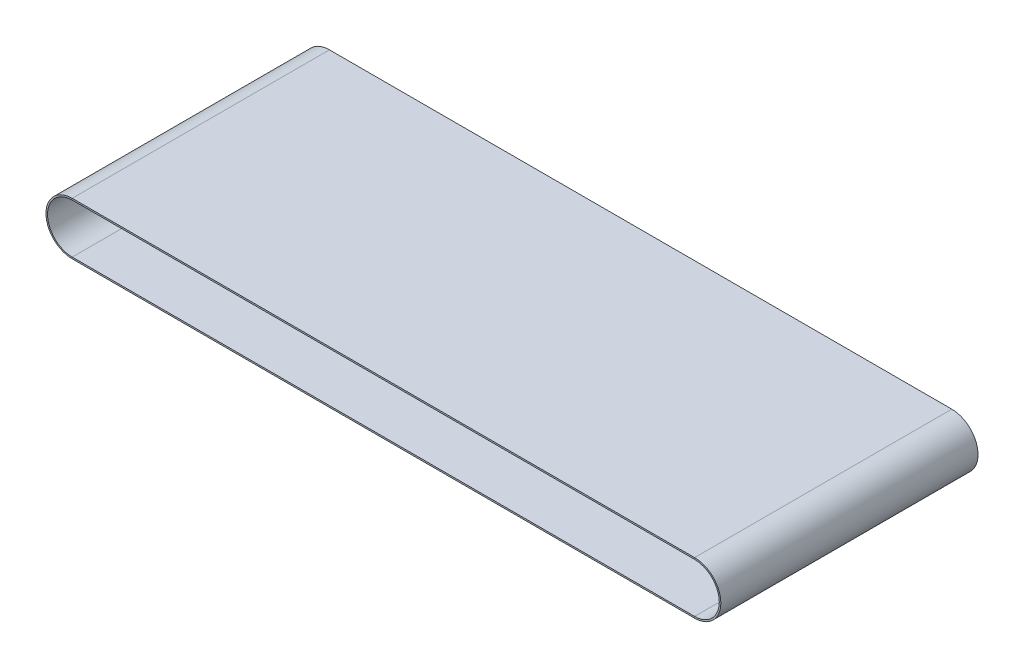
SolidWorks part; units mm, degrees
ref_plane "Front Plane" through (0, 0, 0) normal (0, 0, 1) x (1, 0, 0)
ref_plane "Top Plane" through (0, 0, 0) normal (0, 1, 0) x (1, 0, 0)
ref_plane "Right Plane" through (0, 0, 0) normal (1, 0, 0) x (0, 0, -1)
sketch "Sketch2" plane through (0, 0, 0) normal (0, 0, 1) x (1, 0, 0)
  line L0 (0, 0) -> (1, 0) construction
  line L1 (0, 0) -> (0, 1) construction
  line L2 (0, -24) -> (-605, -24)
  line L3 (-605, 24) -> (0, 24)
  arc A0 (0, 24) -> (0, -24) centre (0, 0) cw
  arc A1 (-605, -24) -> (-605, 24) centre (-605, 0) cw
ref_plane "Plane1" through (-605, 0, 0) normal (1, 0, 0) x (0, 0, -1)
sketch "Sketch4" plane through (-605, 0, 0) normal (1, 0, 0) x (0, 0, -1)
  line L0 (-125, 24) -> (125, 24)
  line L2 (125, 24) -> (125, 25.5)
  line L3 (125, 25.5) -> (-125, 25.5)
  line L5 (-125, 24) -> (-125, 25.5)
  dimension "D2" = 1.5
sweep "Sweep1" add profiles "Sketch4" path "Sketch2"
sketch "Sketch8" plane through (0, 0, 0) normal (0, 0, 1) x (1, 0, 0)
  circle A0 centre (0, 0) radius 25
  circle A1 centre (-605, 0) radius 25
